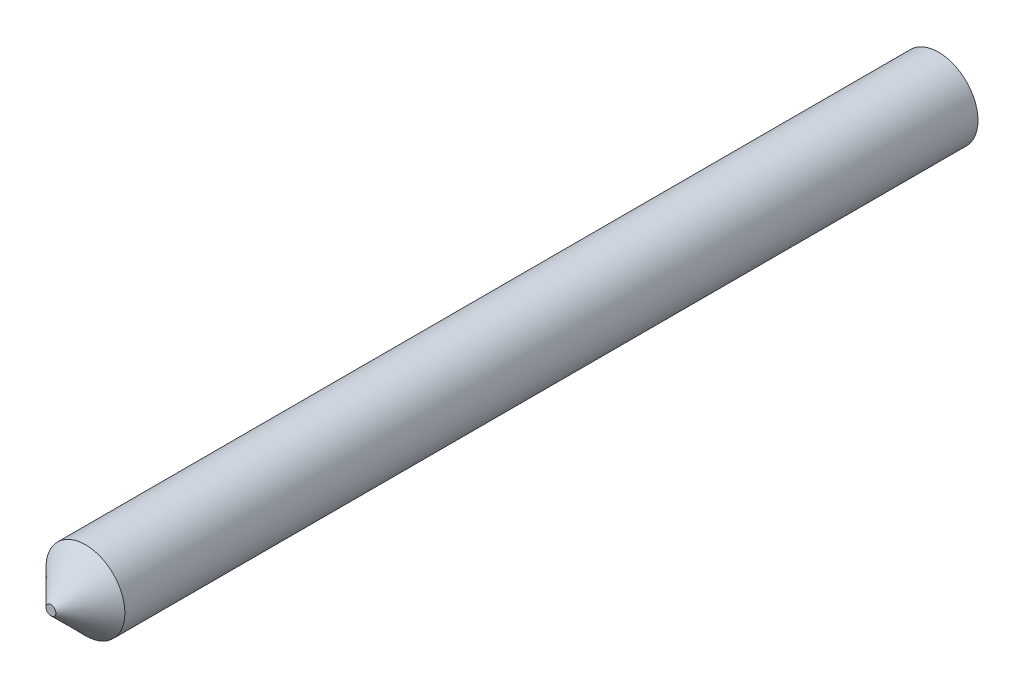
SolidWorks part; units mm, degrees
material "Commercially Pure CP-Ti UNS R50400 (SS)"
ref_plane "Front Plane" through (0, 0, 0) normal (0, 0, 1) x (1, 0, 0)
ref_plane "Top Plane" through (0, 0, 0) normal (0, 1, 0) x (1, 0, 0)
ref_plane "Right Plane" through (0, 0, 0) normal (1, 0, 0) x (0, 0, -1)
sketch "Sketch1" plane through (0, 0, 0) normal (0, 0, 1) x (1, 0, 0)
  circle A0 centre (0, 0) radius 2
  dimension "D1" = 4
extrude "Boss-Extrude1" add sketch "Sketch1" along normal blind 45
chamfer "Chamfer1" distance 1.75 angle 45 1 edges at (2, 0, 45)
